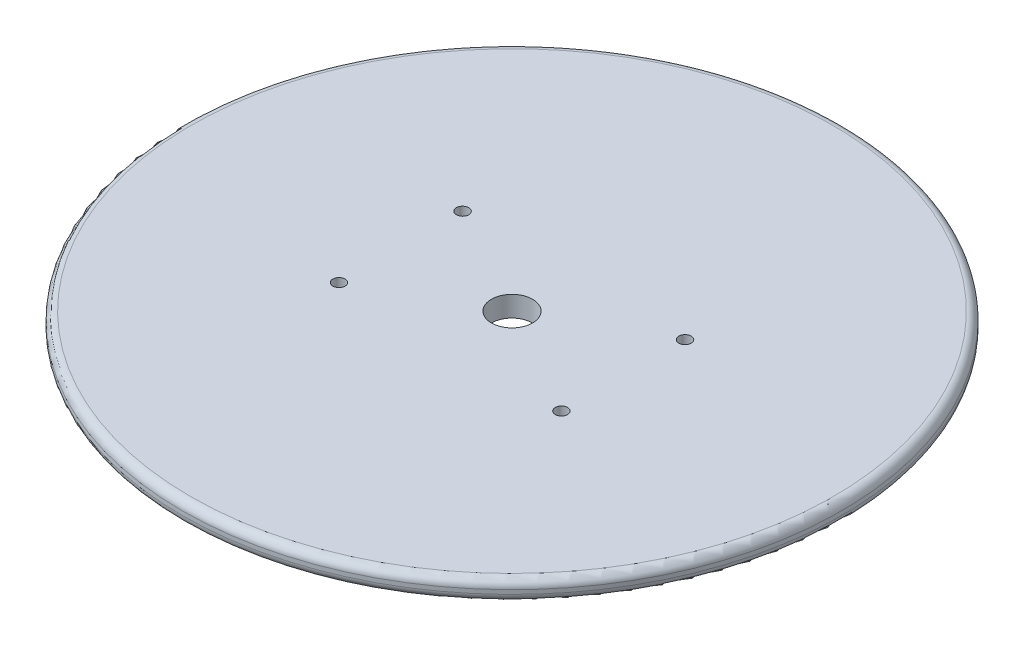
SolidWorks part; units mm, degrees
ref_plane "Front Plane" through (0, 0, 0) normal (0, 0, 1) x (1, 0, 0)
ref_plane "Top Plane" through (0, 0, 0) normal (0, 1, 0) x (1, 0, 0)
ref_plane "Right Plane" through (0, 0, 0) normal (1, 0, 0) x (0, 0, -1)
sketch "Sketch1" plane through (0, 0, 0) normal (0, 1, 0) x (1, 0, 0)
  circle A0 centre (0, 0) radius 80
extrude "Boss-Extrude1" add sketch "Sketch1" along normal blind 5
fillet "Fillet1" radius 2 2 edges at (0, 0, 80) (0, 5, 80)
sketch "Sketch2" plane through (0, 0, 0) normal (0, -1, 0) x (1, 0, 0)
  circle A0 centre (0, 0) radius 5
extrude "Cut-Extrude1" cut sketch "Sketch2" against normal blind 5
sketch "Sketch3" plane through (0, 5, 0) normal (0, 1, 0) x (1, 0, 0)
  line L1 (-27, 15) -> (27, 15)
  line L2 (-27, 15) -> (-27, -15)
  line L3 (-27, -15) -> (27, -15)
  line L4 (27, 15) -> (27, -15)
  line L5 (-27, 15) -> (27, -15) construction
  line L6 (-27, -15) -> (27, 15) construction
  circle A0 centre (-27, 15) radius 1.5
  circle A1 centre (-27, -15) radius 1.5
  circle A2 centre (27, -15) radius 1.5
  circle A3 centre (27, 15) radius 1.5
  point P0 (0, 0)
extrude "Cut-Extrude2" cut sketch "Sketch3" against normal through all contours L1 A0 L2 | L2 A0 L1 | L2 A1 L3 | L3 A1 L2 | L4 A2 L3 | L3 A2 L4 | L1 A3 L4 | L4 A3 L1
